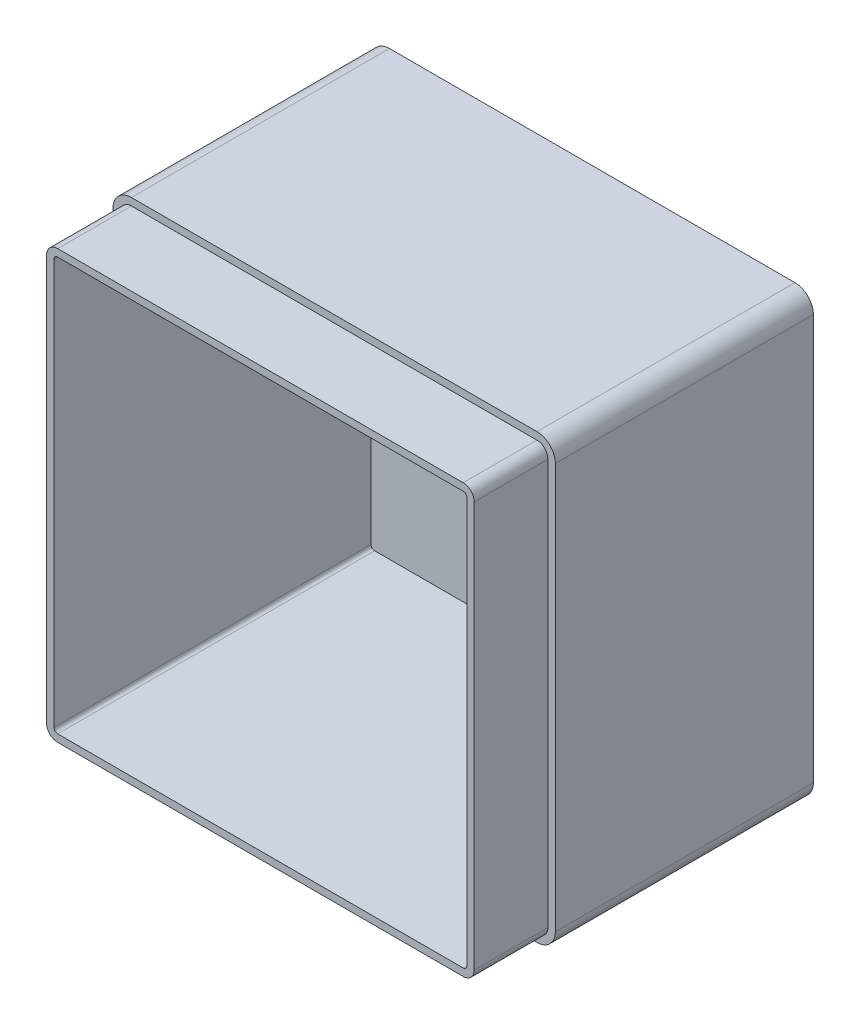
SolidWorks part; units mm, degrees
ref_plane "Front Plane" through (0, 0, 0) normal (0, 0, 1) x (1, 0, 0)
ref_plane "Top Plane" through (0, 0, 0) normal (0, 1, 0) x (1, 0, 0)
ref_plane "Right Plane" through (0, 0, 0) normal (1, 0, 0) x (0, 0, -1)
sketch "Sketch1" plane through (0, 0, 0) normal (0, 0, 1) x (1, 0, 0)
  line L1 (0, 0) -> (120, 0)
  line L2 (0, 0) -> (0, -120)
  line L3 (0, -120) -> (120, -120)
  line L4 (120, 0) -> (120, -120)
  dimension "D1" = 120
  dimension "D2" = 120
extrude "Boss-Extrude1" add sketch "Sketch1" along normal blind 90
fillet "Fillet1" radius 5 4 edges at (0, -120, 45) (0, 0, 45) (120, 0, 45) (120, -120, 45)
shell "Shell1" thickness 4
sketch "Sketch3" plane through (0, 0, 90) normal (0, 0, 1) x (1, 0, 0)
  line L0 (2, -5) -> (2, -115)
  line L1 (5, -118) -> (115, -118)
  line L2 (118, -115) -> (118, -5)
  line L3 (115, -2) -> (5, -2)
  line L4 (0, -5) -> (0, -115)
  line L5 (5, -120) -> (115, -120)
  line L6 (120, -115) -> (120, -5)
  line L7 (115, 0) -> (5, 0)
  line L8 (0, -5) -> (0, -115)
  line L9 (5, -120) -> (115, -120)
  line L10 (120, -115) -> (120, -5)
  line L11 (115, 0) -> (5, 0)
  arc A0 (2, -115) -> (5, -118) centre (5, -115) ccw
  arc A1 (115, -118) -> (118, -115) centre (115, -115) ccw
  arc A2 (118, -5) -> (115, -2) centre (115, -5) ccw
  arc A3 (5, -2) -> (2, -5) centre (5, -5) ccw
  arc A4 (0, -115) -> (5, -120) centre (5, -115) ccw
  arc A5 (115, -120) -> (120, -115) centre (115, -115) ccw
  arc A6 (120, -5) -> (115, 0) centre (115, -5) ccw
  arc A7 (5, 0) -> (0, -5) centre (5, -5) ccw
  arc A8 (0, -115) -> (5, -120) centre (5, -115) ccw
  arc A9 (115, -120) -> (120, -115) centre (115, -115) ccw
  arc A10 (120, -5) -> (115, 0) centre (115, -5) ccw
  arc A11 (5, 0) -> (0, -5) centre (5, -5) ccw
  dimension "D1" = 0
  dimension "D2" = 2
extrude "Cut-Extrude1" cut sketch "Sketch3" against normal blind 20
